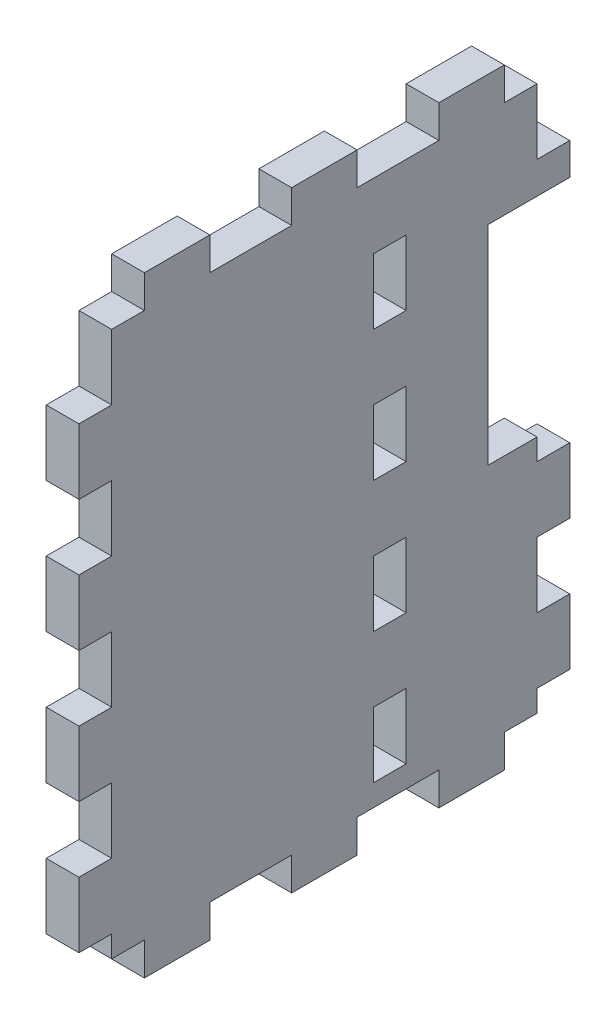
SolidWorks part; units mm, degrees
ref_plane "Front Plane" through (0, 0, 0) normal (0, 0, 1) x (1, 0, 0)
ref_plane "Top Plane" through (0, 0, 0) normal (0, 1, 0) x (1, 0, 0)
ref_plane "Right Plane" through (0, 0, 0) normal (1, 0, 0) x (0, 0, -1)
sketch "Sketch4" plane through (0, 0, 0) normal (0, 0, 1) x (1, 0, 0)
  line L0 (0, 0) -> (40.3547, 419.1) construction
  line L1 (40.3547, 419.1) -> (159.2585, 419.1) construction
  line L2 (159.2585, 419.1) -> (159.2585, 0) construction
  line L3 (159.2585, 0) -> (0, 0) construction
  line L4 (159.2585, -1000) -> (159.2585, 49000) construction
  line L5 (2.0164, 20.9415) -> (40.3547, 419.1) construction
  line L6 (2.0164, 20.9415) -> (41.8323, 17.1077) construction
  line L7 (40.3547, 419.1) -> (80.1706, 415.2662) construction
  line L8 (41.8323, 17.1077) -> (80.1706, 415.2662) construction
  line L9 (64.0085, -1000) -> (64.0085, 49000) construction
  line L10 (-49.0714, 317.5) -> (-124.9206, 324.8034) construction
  line L11 (-26.3513, 414.3375) -> (40.196, 414.3375) construction
  line L12 (-1162.1335, 304.8) -> (48837.8665, 304.8) construction
  line L13 (-126.4915, 292.1) -> (-50.2915, 292.1) construction
  line L14 (-124.9206, 324.8034) -> (-50.2915, 292.1) construction
  line L15 (-49.0714, 317.5) -> (-126.4915, 292.1) construction
  line L16 (40.196, 338.1375) -> (-26.3513, 338.1375) construction
  line L17 (-134.4017, 325.7164) -> (29.8401, 309.9017)
  line L18 (-134.4017, 325.7164) -> (-133.7931, 332.0371)
  line L19 (-133.7931, 332.0371) -> (40.3547, 419.1)
  line L20 (40.3547, 419.1) -> (108.4585, 419.1)
  line L21 (108.4585, 419.1) -> (108.4585, 0) construction
  line L22 (29.8401, 309.9017) -> (0.4102, 4.2603)
  line L23 (0.4102, 4.2603) -> (44.6556, 0)
  line L24 (44.6556, 0) -> (108.4585, 0)
  line L25 (108.4585, 419.1) -> (159.2585, 311.15)
  line L26 (159.2585, 311.15) -> (159.2585, 304.8)
  line L27 (159.2585, 304.8) -> (108.4585, 280.8941)
  line L28 (108.4585, 280.8941) -> (108.4585, 0)
  arc A0 (-124.9206, 324.8034) -> (-26.3513, 414.3375) centre (-26.3513, 315.3123) cw construction
  arc A1 (73.5335, 304.8) -> (40.196, 338.1375) centre (40.196, 304.8) ccw construction
  arc A2 (149.7335, 304.8) -> (40.196, 414.3375) centre (40.196, 304.8) ccw construction
  arc A3 (-49.0714, 317.5) -> (-26.3513, 338.1375) centre (-26.3513, 315.3123) cw construction
  point P7 (57.6585, 400.05)
  point P17 (149.7335, 304.8)
  point P18 (73.5335, 304.8)
  dimension "D9" = 9.525
  dimension "D14" = 25.4
  dimension "D1" = 419.1
  dimension "D2" = 101.6
  dimension "D3" = 19.05
  dimension "D4" = 19.05
  dimension "D5" = 84.5
  dimension "D6" = 40
  dimension "D7" = 400
  dimension "D8" = 95.25
  dimension "D10" = 9.525
  dimension "D11" = 114.3
  dimension "D12" = 76.2
  dimension "D13" = 9.525
  dimension "D15" = 127
  dimension "D16" = 9.525
  dimension "D17" = 209.55
  dimension "D18" = 6.35
  dimension "D19" = 50.8
  dimension "D20" = 44.45
  dimension "D21" = 6.35
sketch "Sketch5" plane through (0, 0, 0) normal (0, 0, 1) x (1, 0, 0)
  line L0 (64.0085, -201000) -> (64.0085, 249000) construction
  line L1 (64.0085, 311.15) -> (57.6585, 311.15)
  line L2 (64.0085, 311.15) -> (64.0085, 192.6118)
  line L3 (64.0085, 192.6118) -> (57.6585, 192.6118)
  line L4 (57.6585, 311.15) -> (57.6585, 192.6118)
  line L5 (-201162.1335, 304.8) -> (248837.8665, 304.8) construction
  line L6 (39.8409, -52.6103) -> (4831.9461, 49715.3046) construction
  line L7 (29.8401, 309.9017) -> (0.4102, 4.2603) construction
  line L8 (64.0085, 198.3798) -> (59.3302, 198.8303) construction
  line L9 (41.8323, 17.1077) -> (80.1706, 415.2662) construction
  point P12 (64.0085, 198.3798)
  dimension "D1" = 6.35
  dimension "D2" = 44.7
  dimension "D3" = 6.35
  dimension "D4" = 6.35
extrude "Boss-Extrude1" add sketch "Sketch5" along normal blind 95.25
sketch "Sketch7" plane through (64.0085, 0, 0) normal (1, 0, 0) x (0, 0, -1)
  line L0 (-95.25, 192.6118) -> (-95.25, 311.15) construction
  line L1 (-95.25, 304.8) -> (-88.9, 304.8)
  line L2 (-95.25, 304.8) -> (-95.25, 292.1)
  line L3 (-95.25, 292.1) -> (-88.9, 292.1)
  line L4 (-88.9, 304.8) -> (-88.9, 292.1)
  line L5 (0, 192.6118) -> (0, 311.15) construction
  line L6 (0, 304.8) -> (-6.35, 304.8)
  line L7 (0, 304.8) -> (0, 292.1)
  line L8 (0, 292.1) -> (-6.35, 292.1)
  line L9 (-6.35, 304.8) -> (-6.35, 292.1)
  line L10 (-95.25, 311.15) -> (0, 311.15) construction
  dimension "D1" = 6.35
  dimension "D2" = 12.7
  dimension "D3" = 6.35
extrude "Cut-Extrude1" cut sketch "Sketch7" against normal through all
pattern_linear "LPattern1" count 5 spacing 25.4 along (0, -1, 0) of "Cut-Extrude1"
sketch "Sketch8" plane through (64.0085, 0, 0) normal (1, 0, 0) x (0, 0, -1)
  line L0 (0, 279.4) -> (0, 292.1) construction
  line L1 (-38.1, 317.5) -> (-31.75, 317.5)
  line L2 (-38.1, 317.5) -> (-38.1, 304.8)
  line L3 (-38.1, 304.8) -> (-31.75, 304.8)
  line L4 (-31.75, 317.5) -> (-31.75, 304.8)
  line L6 (-95.25, 311.15) -> (0, 311.15) construction
  dimension "D1" = 12.7
  dimension "D2" = 6.35
  dimension "D3" = 31.75
  dimension "D4" = 6.35
extrude "Cut-Extrude2" cut sketch "Sketch8" against normal through all
pattern_linear "LPattern2" count 5 spacing 25.4 along (0, -1, 0) of "Cut-Extrude2"
sketch "Sketch9" plane through (0, 0, 0) normal (0, 0, -1) x (-1, 0, 0)
  line L0 (-42.1408, 277.931) -> (-81.0698, 292.1)
  line L1 (-81.0698, 292.1) -> (-81.0698, 237.6469)
  line L2 (-81.0698, 237.6469) -> (-41.263, 255.8285)
  line L3 (-64.0085, 254) -> (-64.0085, 266.7) construction
  line L4 (-64.0085, 311.15) -> (-57.6585, 311.15) construction
  line L5 (-46.2285, 266.7) -> (-46.2285, 248.92) construction
  line L6 (-46.2285, 248.92) -> (-56.3885, 248.92) construction
  line L7 (-57.6585, 266.7) -> (-64.0085, 266.7) construction
  line L8 (-87.4101, 357.9466) -> (4704.8775, -49411.8633) construction
  line L9 (-41.8323, 17.1077) -> (-80.1706, 415.2662) construction
  line L10 (201162.1335, 304.8) -> (-248837.8665, 304.8) construction
  arc A0 (-42.1408, 277.931) -> (-41.263, 255.8285) centre (-46.2285, 266.7) cw
  dimension "D1" = 17.78
  dimension "D2" = 44.45
  dimension "D3" = 17.78
  dimension "D4" = 10.16
  dimension "D5" = 20
  dimension "D6" = 12.7
  dimension "D7" = 12.7
extrude "Cut-Extrude3" cut sketch "Sketch9" against normal blind 15.875
sketch "Sketch10" plane through (64.0085, 0, 0) normal (1, 0, 0) x (0, 0, -1)
  line L0 (-95.25, 311.15) -> (-38.1, 311.15) construction
  line L1 (-95.25, 311.15) -> (-82.55, 311.15)
  line L2 (-95.25, 311.15) -> (-95.25, 304.8)
  line L3 (-95.25, 304.8) -> (-82.55, 304.8)
  line L4 (-82.55, 311.15) -> (-82.55, 304.8)
  line L5 (-69.85, 311.15) -> (-53.975, 311.15)
  line L6 (-69.85, 311.15) -> (-69.85, 304.8)
  line L7 (-69.85, 304.8) -> (-53.975, 304.8)
  line L8 (-53.975, 311.15) -> (-53.975, 304.8)
  line L9 (-47.625, 192.6118) -> (-47.625, 311.15) construction
  line L10 (-41.275, 311.15) -> (-25.4, 311.15)
  line L11 (-41.275, 311.15) -> (-41.275, 304.8)
  line L12 (-41.275, 304.8) -> (-25.4, 304.8)
  line L13 (-25.4, 311.15) -> (-25.4, 304.8)
  line L14 (0, 311.15) -> (-12.7, 311.15)
  line L15 (0, 311.15) -> (0, 304.8)
  line L16 (0, 304.8) -> (-12.7, 304.8)
  line L17 (-12.7, 311.15) -> (-12.7, 304.8)
  line L18 (-88.9, 192.6118) -> (-6.35, 192.6118) construction
  dimension "D1" = 12.7
  dimension "D2" = 12.7
  dimension "D3" = 12.7
  dimension "D4" = 12.7
  dimension "D5" = 6.35
extrude "Cut-Extrude4" cut sketch "Sketch10" against normal through all
sketch "Sketch11" plane through (64.0085, 0, 0) normal (1, 0, 0) x (0, 0, -1)
  line L0 (-88.9, 192.6118) -> (-6.35, 192.6118) construction
  line L1 (-88.9, 192.6118) -> (-82.55, 192.6118)
  line L2 (-88.9, 192.6118) -> (-88.9, 198.9999)
  line L3 (-88.9, 198.9999) -> (-82.55, 198.9999)
  line L4 (-82.55, 192.6118) -> (-82.55, 198.9999)
  line L5 (-69.85, 192.6118) -> (-53.975, 192.6118)
  line L6 (-69.85, 192.6118) -> (-69.85, 198.9999)
  line L7 (-69.85, 198.9999) -> (-53.975, 198.9999)
  line L8 (-53.975, 192.6118) -> (-53.975, 198.9999)
  line L9 (-82.55, 304.8) -> (-82.55, 311.15) construction
  line L10 (-41.275, 192.6118) -> (-25.4, 192.6118)
  line L11 (-41.275, 192.6118) -> (-41.275, 198.9999)
  line L12 (-41.275, 198.9999) -> (-25.4, 198.9999)
  line L13 (-25.4, 192.6118) -> (-25.4, 198.9999)
  line L14 (-6.35, 192.6118) -> (-12.7, 192.6118)
  line L15 (-6.35, 192.6118) -> (-6.35, 198.9999)
  line L16 (-6.35, 198.9999) -> (-12.7, 198.9999)
  line L17 (-12.7, 192.6118) -> (-12.7, 198.9999)
  line L18 (-69.85, 311.15) -> (-69.85, 304.8) construction
  line L19 (-41.275, 311.15) -> (-41.275, 304.8) construction
  line L20 (-12.7, 311.15) -> (-12.7, 304.8) construction
  line L22 (-41.275, 304.8) -> (-25.4, 304.8) construction
  dimension "D1" = 6.3881
extrude "Cut-Extrude5" cut sketch "Sketch11" against normal through all
sketch "Sketch13" plane through (0, 0, 0) normal (0, 0, -1) x (-1, 0, 0)
  line L1 (-64.0085, 285.8902) -> (-57.6585, 285.8902)
  line L2 (-64.0085, 285.8902) -> (-64.0085, 283.579)
  line L3 (-64.0085, 283.579) -> (-57.6585, 283.579)
  line L4 (-57.6585, 285.8902) -> (-57.6585, 283.579)
  line L5 (-64.0085, 245.4396) -> (-57.6585, 245.4396)
  line L6 (-64.0085, 245.4396) -> (-64.0085, 248.3399)
  line L7 (-64.0085, 248.3399) -> (-57.6585, 248.3399)
  line L8 (-57.6585, 245.4396) -> (-57.6585, 248.3399)
extrude "Cut-Extrude6" cut sketch "Sketch13" against normal blind 15.875
